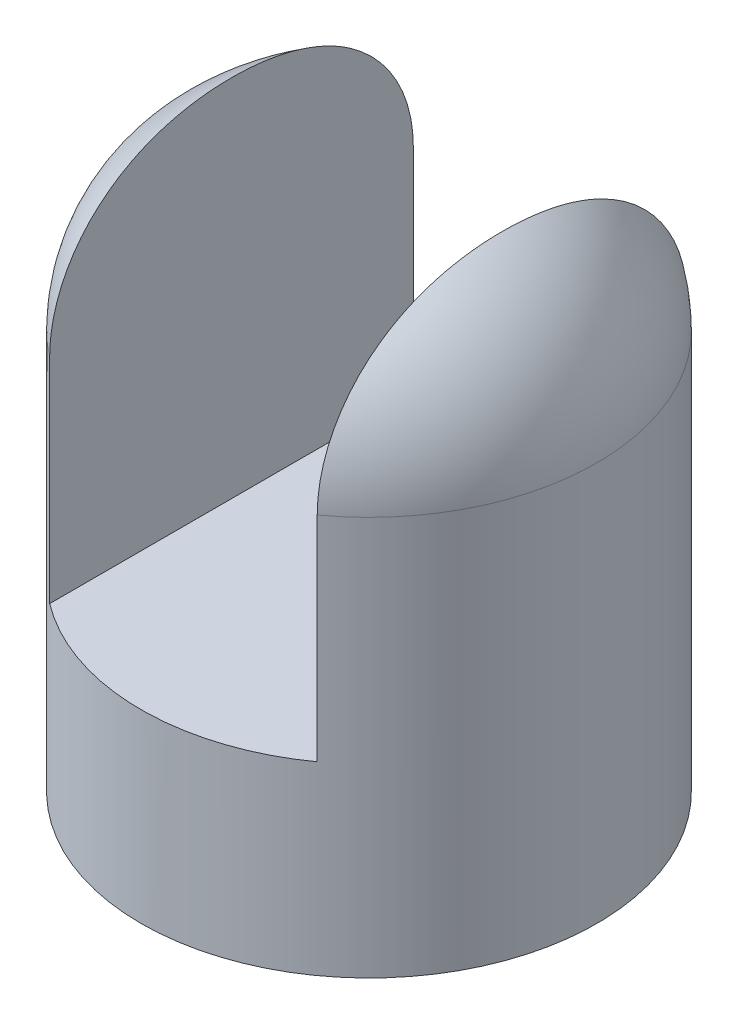
SolidWorks part; units mm, degrees
ref_plane "Płaszczyzna przednia" through (0, 0, 0) normal (0, 0, 1) x (1, 0, 0)
ref_plane "Płaszczyzna górna" through (0, 0, 0) normal (0, 1, 0) x (1, 0, 0)
ref_plane "Płaszczyzna prawa" through (0, 0, 0) normal (1, 0, 0) x (0, 0, -1)
sketch "Szkic2" plane through (0, 0, 0) normal (0, 1, 0) x (1, 0, 0)
  circle A0 centre (0, 0) radius 80
extrude "Dodanie-wyciągnięcie2" add sketch "Szkic2" along normal blind 200
fillet "Zaokrąglenie1" radius 60 1 edges at (0, 200, 80)
sketch "Szkic5" plane through (0, 200, 0) normal (0, 1, 0) x (1, 0, 0)
  line L7 (46.75, 0) -> (46.75, 80.0001)
  line L8 (46.75, 80.0001) -> (-48.25, 80.0001)
  line L9 (-48.25, 0) -> (-48.25, 80.0001)
  line L11 (46.75, 0) -> (46.75, -80.0003)
  line L12 (46.75, -80.0003) -> (-48.25, -80.0003)
  line L13 (-48.25, 0) -> (-48.25, -80.0003)
  point P5 (0, 0)
  dimension "D1" = 95
extrude "Wytnij-wyciągnięcie1" cut sketch "Szkic5" against normal blind 135
sketch "Szkic6" plane through (-48.25, 0, 0) normal (1, 0, 0) x (0, 0, -1)
  circle A0 centre (0, 132.9126) radius 60
sketch "Szkic7" plane through (46.75, 0, 0) normal (-1, 0, 0) x (0, 0, 1)
  circle A0 centre (0, 132.9067) radius 60
